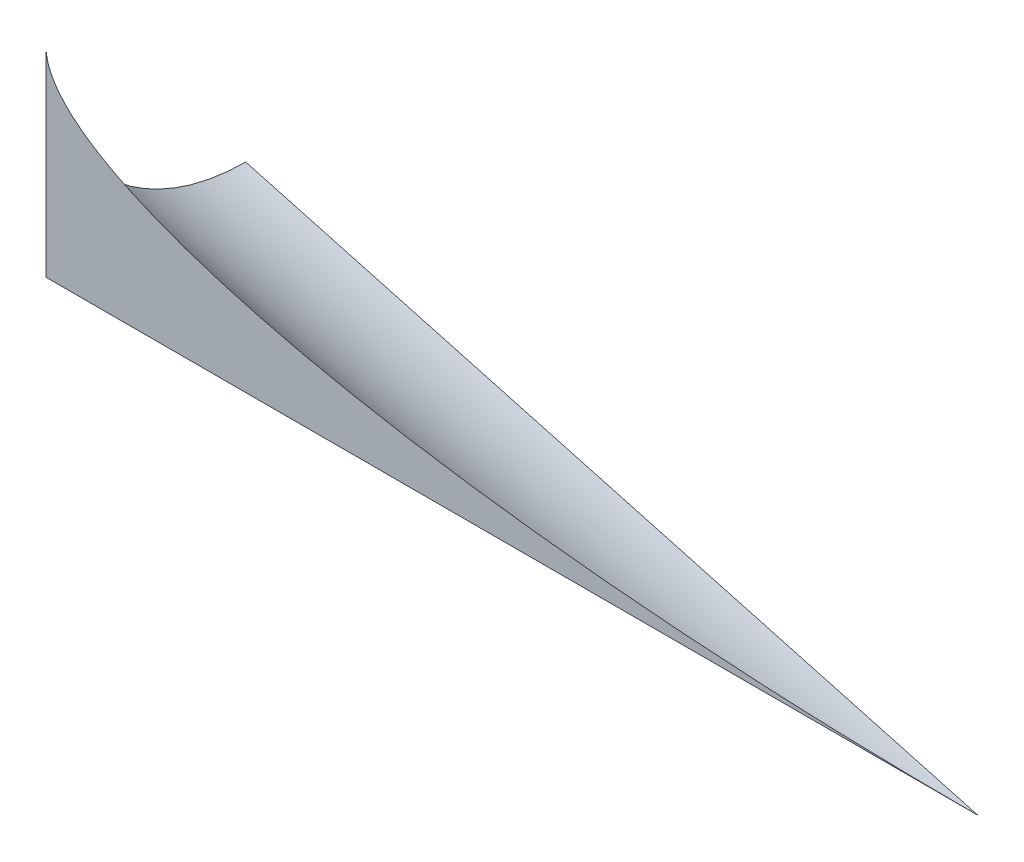
SolidWorks part; units mm, degrees
ref_plane "Plan de face" through (0, 0, 0) normal (0, 0, 1) x (1, 0, 0)
ref_plane "Plan de dessus" through (0, 0, 0) normal (0, 1, 0) x (1, 0, 0)
ref_plane "Plan de droite" through (0, 0, 0) normal (1, 0, 0) x (0, 0, -1)
sketch3d "Esquisse3D2"
  line L0 (0, 0, 0) -> (70, 0, 0)
  line L1 (0, 0, 0) -> (0, 15, 0)
  line L2 (0, 15, 0) -> (70, 0, 0)
  line L3 (0, 0, 0) -> (0, 0, -15)
  line L4 (0, 0, -15) -> (70, 0, 0)
  arc A0 (0, 0, -15) -> (0, 15, 0) centre (0, 15, -15) cw
  point P6 (-15, 15, -15)
  dimension "D1" = 70
  dimension "D2" = 15
  dimension "D3" = 15
sketch "Esquisse1" plane through (0, 0, 0) normal (1, 0, 0) x (0, 0, -1)
  line L1 (0, 0) -> (15, 0)
  line L2 (0, 0) -> (0, 15)
  line L3 (0, 15) -> (15, 15)
  line L4 (15, 0) -> (15, 15)
  dimension "D1" = 15
extrude "Boss.-Extru.1" add sketch "Esquisse1" along normal blind 70
sketch "Esquisse2" plane through (0, 0, 0) normal (-1, 0, 0) x (0, 0, 1)
  line L0 (0, 0) -> (-15, 0) construction
  line L1 (0, 0) -> (0, 15) construction
  line L2 (0, 0) -> (-15, 0) construction
  line L3 (0, 0) -> (0, 15) construction
  line L4 (0, 0) -> (0, 15)
  line L5 (0, 15) -> (-15, 15)
  line L6 (-15, 15) -> (-15, 0)
  line L7 (-15, 0) -> (0, 0)
  line L8 (0, 0) -> (0, 15) construction
  line L9 (0, 15) -> (-15, 15)
  line L10 (-15, 15) -> (-15, 0)
  line L11 (-15, 0) -> (0, 0) construction
  arc A0 (-15, 0) -> (0, 15) centre (-15, 15) ccw construction
  arc A1 (-15, 0) -> (0, 15) centre (-15, 15) ccw
  dimension "D1" = 0
sketch3d "Esquisse3D3"
  line L0 (0, 0, -15) -> (70, 0, 0)
  point P4 (0, 0, 0)
  point P5 (0, 15, 0)
  point P7 (0, 0, 0)
  point P8 (0, 0, -15)
sweep "Enlèvement de matière-Balayage2" cut profiles "Esquisse2" path "Esquisse3D3"
